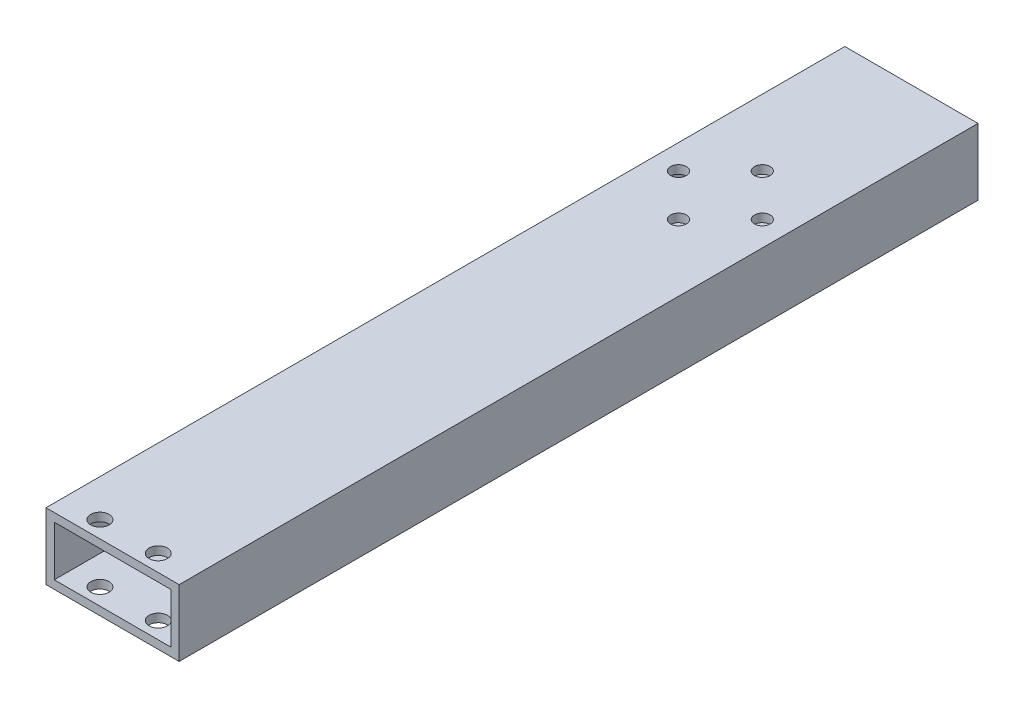
SolidWorks part; units mm, degrees
material "6061 Alloy"
ref_plane "Front Plane" through (0, 0, 0) normal (0, 0, 1) x (1, 0, 0)
ref_plane "Top Plane" through (0, 0, 0) normal (0, 1, 0) x (1, 0, 0)
ref_plane "Right Plane" through (0, 0, 0) normal (1, 0, 0) x (0, 0, -1)
sketch "Sketch1" plane through (0, 0, 0) normal (0, 0, 1) x (1, 0, 0)
  line L1 (-12.7, 6.35) -> (12.7, 6.35)
  line L2 (-12.7, 6.35) -> (-12.7, -6.35)
  line L3 (-12.7, -6.35) -> (12.7, -6.35)
  line L4 (12.7, 6.35) -> (12.7, -6.35)
  point P4 (-12.7, 0)
  point P6 (0, 6.35)
  dimension "D1" = 12.7
  dimension "D2" = 25.4
extrude "Boss-Extrude1" add sketch "Sketch1" along normal blind 127
sketch "Sketch4" plane through (0, 0, 0) normal (0, 0, -1) x (-1, 0, 0)
  line L0 (-12.7, -6.35) -> (-12.7, 6.35) construction
  line L1 (-11.1125, 4.7625) -> (11.1125, 4.7625)
  line L2 (-11.1125, 4.7625) -> (-11.1125, -4.7625)
  line L3 (-11.1125, -4.7625) -> (11.1125, -4.7625)
  line L4 (11.1125, 4.7625) -> (11.1125, -4.7625)
  line L5 (-12.7, 6.35) -> (12.7, 6.35) construction
  line L6 (12.7, -6.35) -> (-12.7, -6.35) construction
  line L7 (12.7, 6.35) -> (12.7, -6.35) construction
  dimension "D1" = 1.5875
  dimension "D2" = 1.5875
  dimension "D3" = 1.5875
  dimension "D4" = 1.5875
extrude "Cut-Extrude1" cut sketch "Sketch4" against normal through all
sketch "Sketch5" plane through (0, 6.35, 0) normal (0, 1, 0) x (1, 0, 0)
  line L2 (12.7, -127) -> (-12.7, -127) construction
  line L3 (-12.7, -127) -> (-12.7, 0) construction
  circle A0 centre (-5.588, -123.825) radius 1.7526
  circle A1 centre (5.5372, -123.825) radius 1.7526
  dimension "D1" = 3.5052
  dimension "D2" = 3.5052
  dimension "D3" = 11.1252
  dimension "D4" = 7.112
  dimension "D5" = 3.175
  dimension "D6" = 3.175
extrude "Cut-Extrude2" cut sketch "Sketch5" against normal through all both and the other way through all
sketch "Sketch6" plane through (0, -6.35, 0) normal (0, -1, 0) x (-1, 0, 0)
  line L2 (12.7, -127) -> (-12.7, -127) construction
  circle A0 centre (8, -11.05) radius 1.5
  circle A1 centre (-8, -11.05) radius 1.5
  circle A2 centre (0, -11.05) radius 8 construction
  circle A3 centre (0, -3.05) radius 1.5
  circle A4 centre (0, -19.05) radius 1.5
  dimension "D1" = 3
  dimension "D6" = 16
  dimension "D7" = 3
  dimension "D8" = 3
  dimension "D9" = 107.95
extrude "Cut-Extrude3" cut sketch "Sketch6" against normal through all both contours A3 | A1 | A4 | A0
sketch "Sketch7" plane through (0, 0, 0) normal (0, 0, -1) x (-1, 0, 0)
  line L1 (-12.7, 6.35) -> (12.7, 6.35)
  line L2 (-12.7, 6.35) -> (-12.7, -6.35)
  line L3 (-12.7, -6.35) -> (12.7, -6.35)
  line L4 (12.7, 6.35) -> (12.7, -6.35)
  line L5 (-11.1125, 4.7625) -> (11.1125, 4.7625)
  line L6 (-11.1125, 4.7625) -> (-11.1125, -4.7625)
  line L7 (-11.1125, -4.7625) -> (11.1125, -4.7625)
  line L8 (11.1125, 4.7625) -> (11.1125, -4.7625)
extrude "Boss-Extrude2" add sketch "Sketch7" along normal blind 25.4
